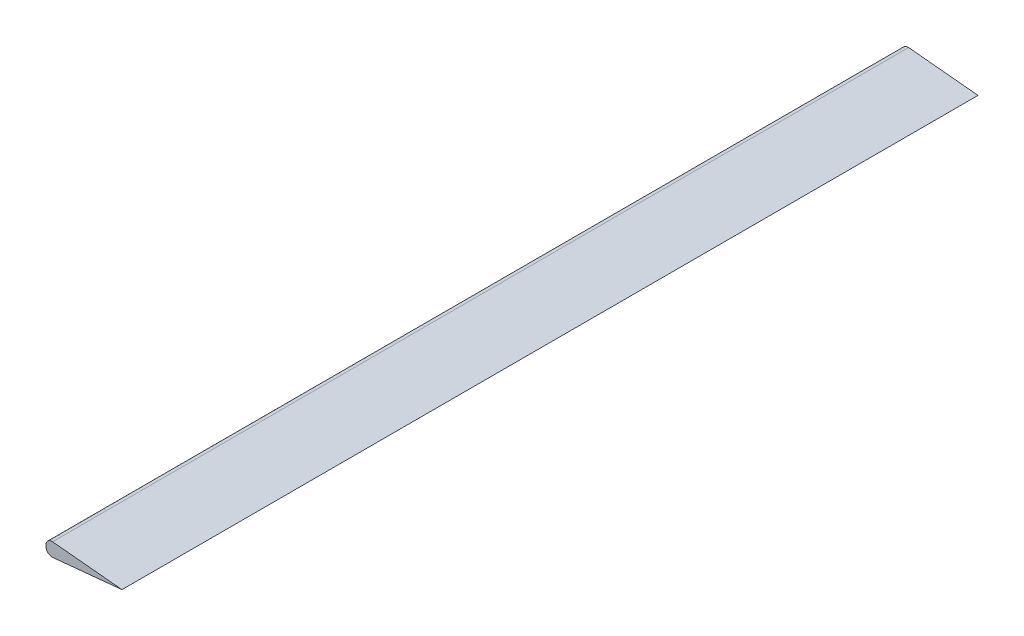
SolidWorks part; units mm, degrees
ref_plane "Front Plane" through (0, 0, 0) normal (0, 0, 1) x (1, 0, 0)
ref_plane "Top Plane" through (0, 0, 0) normal (0, 1, 0) x (1, 0, 0)
ref_plane "Right Plane" through (0, 0, 0) normal (1, 0, 0) x (0, 0, -1)
sketch "Sketch1" plane through (0, 0, 0) normal (0, 0, 1) x (1, 0, 0)
  line L0 (0, 4.6825) -> (0, -4.6825)
  line L1 (0, 0) -> (48.1482, 0) construction
  line L2 (0, 4.6825) -> (48.1482, 0)
  line L3 (48.1482, 0) -> (0, -4.6825)
  point P4 (0, 0)
  dimension "D1" = 9.365
  dimension "D2" = 48.1482
extrude "Boss-Extrude1" add sketch "Sketch1" along normal blind 542.544
fillet "Fillet1" radius 3.81 2 edges at (0, -4.6825, 271.272) (0, 4.6825, 271.272)
